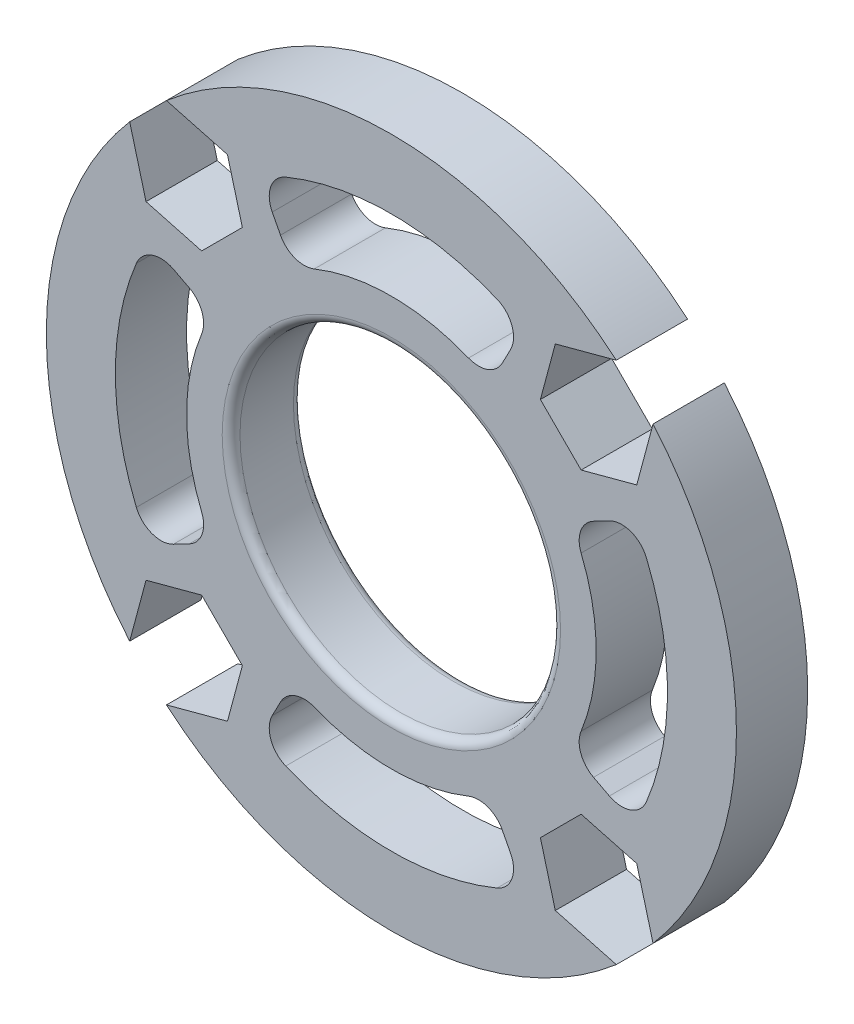
SolidWorks part; units mm, degrees
ref_plane "Front Plane" through (0, 0, 0) normal (0, 0, 1) x (1, 0, 0)
ref_plane "Top Plane" through (0, 0, 0) normal (0, 1, 0) x (1, 0, 0)
ref_plane "Right Plane" through (0, 0, 0) normal (1, 0, 0) x (0, 0, -1)
sketch "Sketch1" plane through (0, 0, 0) normal (0, 0, 1) x (1, 0, 0)
  line L0 (0, 0) -> (0, 19.375) construction
  line L1 (6.6897, 12.241) -> (6.226, 11.3504)
  line L2 (-6.6897, 12.241) -> (-6.226, 11.3504)
  line L3 (12.241, 6.6897) -> (11.3504, 6.226)
  line L4 (12.241, -6.6897) -> (11.3504, -6.226)
  line L5 (6.6897, -12.241) -> (6.226, -11.3504)
  line L6 (-6.6897, -12.241) -> (-6.226, -11.3504)
  line L7 (-12.241, -6.6897) -> (-11.3504, -6.226)
  line L8 (-12.241, 6.6897) -> (-11.3504, 6.226)
  circle A0 centre (0, 0) radius 19.375
  circle A1 centre (0, 0) radius 9
  arc A2 (4.3307, 10.6534) -> (-4.3307, 10.6534) centre (0, 0) ccw
  arc A3 (5.9334, 14.3194) -> (-5.9334, 14.3194) centre (0, 0) ccw
  arc A4 (6.6897, 12.241) -> (5.9334, 14.3194) centre (5.3592, 12.9336) ccw
  arc A5 (6.226, 11.3504) -> (4.3307, 10.6534) centre (4.8955, 12.043) cw
  arc A6 (-6.226, 11.3504) -> (-4.3307, 10.6534) centre (-4.8955, 12.043) ccw
  arc A7 (-6.6897, 12.241) -> (-5.9334, 14.3194) centre (-5.3592, 12.9336) cw
  arc A8 (10.6534, -4.3307) -> (10.6534, 4.3307) centre (0, 0) ccw
  arc A9 (11.3504, 6.226) -> (10.6534, 4.3307) centre (12.043, 4.8955) ccw
  arc A10 (12.241, 6.6897) -> (14.3194, 5.9334) centre (12.9336, 5.3592) cw
  arc A11 (14.3194, -5.9334) -> (14.3194, 5.9334) centre (0, 0) ccw
  arc A12 (12.241, -6.6897) -> (14.3194, -5.9334) centre (12.9336, -5.3592) ccw
  arc A13 (11.3504, -6.226) -> (10.6534, -4.3307) centre (12.043, -4.8955) cw
  arc A14 (-4.3307, -10.6534) -> (4.3307, -10.6534) centre (0, 0) ccw
  arc A15 (6.226, -11.3504) -> (4.3307, -10.6534) centre (4.8955, -12.043) ccw
  arc A16 (6.6897, -12.241) -> (5.9334, -14.3194) centre (5.3592, -12.9336) cw
  arc A17 (-5.9334, -14.3194) -> (5.9334, -14.3194) centre (0, 0) ccw
  arc A18 (-6.6897, -12.241) -> (-5.9334, -14.3194) centre (-5.3592, -12.9336) ccw
  arc A19 (-6.226, -11.3504) -> (-4.3307, -10.6534) centre (-4.8955, -12.043) cw
  arc A20 (-10.6534, 4.3307) -> (-10.6534, -4.3307) centre (0, 0) ccw
  arc A21 (-11.3504, -6.226) -> (-10.6534, -4.3307) centre (-12.043, -4.8955) ccw
  arc A22 (-12.241, -6.6897) -> (-14.3194, -5.9334) centre (-12.9336, -5.3592) cw
  arc A23 (-14.3194, 5.9334) -> (-14.3194, -5.9334) centre (0, 0) ccw
  arc A24 (-12.241, 6.6897) -> (-14.3194, 5.9334) centre (-12.9336, 5.3592) ccw
  arc A25 (-11.3504, 6.226) -> (-10.6534, 4.3307) centre (-12.043, 4.8955) cw
  point P56 (0, 0)
  dimension "D1" = 38.75
  dimension "D2" = 18
  dimension "D3" = 4
  dimension "D4" = 23
  dimension "D5" = 1.5
  dimension "D6" = 55
  dimension "D7" = 4
extrude "Boss-Extrude1" add sketch "Sketch1" along normal blind 4
sketch "Sketch2" plane through (0, 0, 0) normal (0, 0, -1) x (-1, 0, 0)
  line L0 (0, 0) -> (23.1637, 0) construction
  line L2 (19.8581, 19.8581) -> (0, 0) construction
  line L3 (10.6537, -8.3675) -> (8.3675, -10.6537)
  line L4 (13.7767, 9.2043) -> (14.6135, 12.3273)
  line L5 (14.6135, 12.3273) -> (12.3273, 14.6135)
  line L6 (12.3273, 14.6135) -> (9.2043, 13.7767)
  line L7 (9.2043, 13.7767) -> (8.3675, 10.6537)
  line L8 (8.3675, 10.6537) -> (10.6537, 8.3675)
  line L9 (10.6537, 8.3675) -> (13.7767, 9.2043)
  line L10 (8.3675, -10.6537) -> (9.2043, -13.7767)
  line L11 (9.2043, -13.7767) -> (12.3273, -14.6135)
  line L12 (12.3273, -14.6135) -> (14.6135, -12.3273)
  line L13 (14.6135, -12.3273) -> (13.7767, -9.2043)
  line L14 (13.7767, -9.2043) -> (10.6537, -8.3675)
  line L15 (-8.3675, -10.6537) -> (-10.6537, -8.3675)
  line L16 (-10.6537, -8.3675) -> (-13.7767, -9.2043)
  line L17 (-13.7767, -9.2043) -> (-14.6135, -12.3273)
  line L18 (-14.6135, -12.3273) -> (-12.3273, -14.6135)
  line L19 (-12.3273, -14.6135) -> (-9.2043, -13.7767)
  line L20 (-9.2043, -13.7767) -> (-8.3675, -10.6537)
  line L21 (-10.6537, 8.3675) -> (-8.3675, 10.6537)
  line L22 (-8.3675, 10.6537) -> (-9.2043, 13.7767)
  line L23 (-9.2043, 13.7767) -> (-12.3273, 14.6135)
  line L24 (-12.3273, 14.6135) -> (-14.6135, 12.3273)
  line L25 (-14.6135, 12.3273) -> (-13.7767, 9.2043)
  line L26 (-13.7767, 9.2043) -> (-10.6537, 8.3675)
  circle A0 centre (0, 0) radius 16.25 construction
  circle A1 centre (11.4905, 11.4905) radius 2.8 construction
  point P34 (0, 0)
  dimension "D2" = 32.5
  dimension "D1" = 45
  dimension "D3" = 5.6
  dimension "D4" = 4
extrude "Cut-Extrude1" cut sketch "Sketch2" against normal blind 4
fillet "Fillet1" radius 0.5 2 edges at (9, 0, 4) (9, 0, 0)
sketch "Sketch3" plane through (0, 0, 4) normal (0, 0, 1) x (1, 0, 0)
  line L0 (-13.7767, 9.2043) -> (-15.4503, 15.4503)
  line L1 (-13.7767, 9.2043) -> (-14.6135, 12.3273) construction
  line L2 (-15.4503, 15.4503) -> (-9.2043, 13.7767)
  line L3 (-12.3273, 14.6135) -> (-9.2043, 13.7767) construction
  line L4 (-13.7767, 9.2043) -> (-9.2043, 13.7767)
  line L5 (9.2043, 13.7767) -> (15.4503, 15.4503)
  line L6 (15.4503, 15.4503) -> (13.7767, 9.2043)
  line L7 (9.2043, 13.7767) -> (13.7767, 9.2043)
  line L8 (13.7767, -9.2043) -> (15.4503, -15.4503)
  line L9 (15.4503, -15.4503) -> (9.2043, -13.7767)
  line L10 (13.7767, -9.2043) -> (9.2043, -13.7767)
  line L11 (-9.2043, -13.7767) -> (-15.4503, -15.4503)
  line L12 (-15.4503, -15.4503) -> (-13.7767, -9.2043)
  line L13 (-9.2043, -13.7767) -> (-13.7767, -9.2043)
  point P21 (0, 0)
  dimension "D1" = 4
extrude "Cut-Extrude2" cut sketch "Sketch3" against normal blind 10
equation "\"D3@Sketch2\"=5.4+.2"
